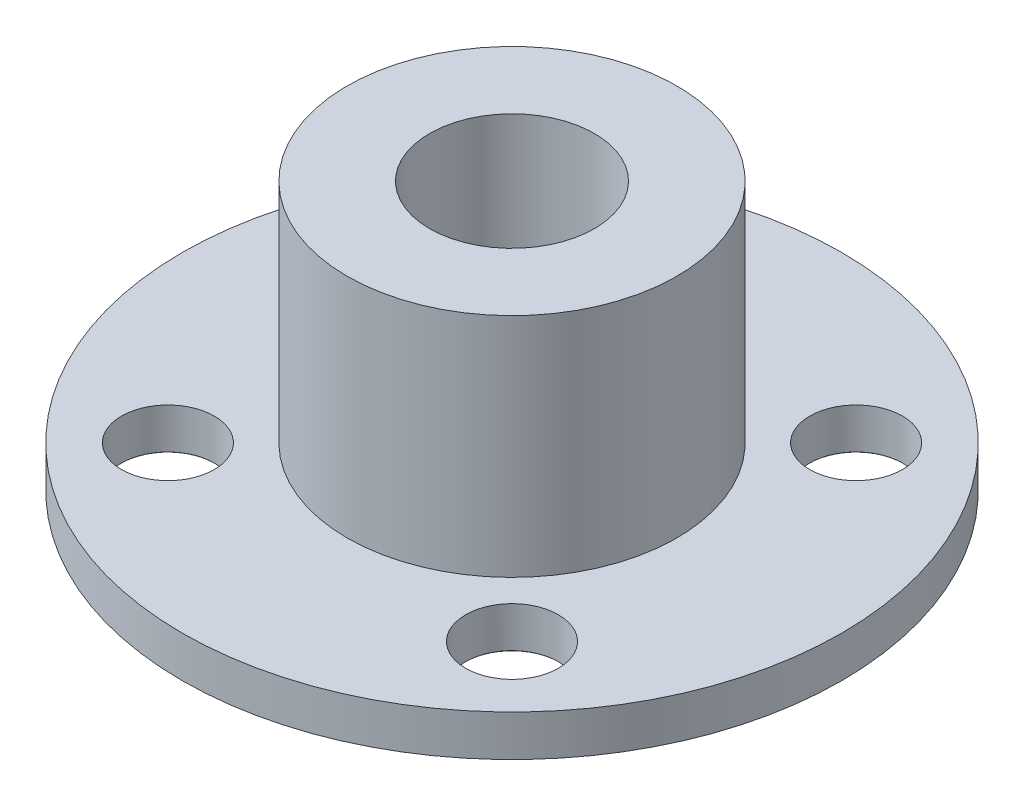
SolidWorks part; units mm, degrees
ref_plane "Front Plane" through (0, 0, 0) normal (0, 0, 1) x (1, 0, 0)
ref_plane "Top Plane" through (0, 0, 0) normal (0, 1, 0) x (1, 0, 0)
ref_plane "Right Plane" through (0, 0, 0) normal (1, 0, 0) x (0, 0, -1)
sketch "Sketch1" plane through (0, 0, 0) normal (0, 1, 0) x (1, 0, 0)
  circle A0 centre (0, 0) radius 16
  circle A1 centre (0, 0) radius 4
  dimension "D1" = 32
  dimension "D2" = 8
extrude "Boss-Extrude1" add sketch "Sketch1" along normal blind 2
sketch "Sketch2" plane through (0, 2, 0) normal (0, 1, 0) x (1, 0, 0)
  circle A0 centre (0, 0) radius 4
  circle A1 centre (0, 0) radius 8
  dimension "D1" = 8
  dimension "D2" = 16
extrude "Boss-Extrude2" add sketch "Sketch2" along normal blind 11 contours A1 | A0
hole_wizard "M4 Clearance Hole1" positions "Sketch5" profile "Sketch4" hole size "M4" standard "ANSI Metric"
sketch "Sketch5" plane through (0, 0, 0) normal (0, -1, 0) x (-1, 0, 0)
  point P0 (-8.35, 8.35)
  point P2 (8.35, 8.35)
  point P4 (8.35, -8.35)
  point P6 (-8.35, -8.35)
  dimension "D1" = 8.35
  dimension "D2" = 8.35
  dimension "D3" = 8.35
  dimension "D4" = 8.35
sketch "Sketch4" plane through (8.35, 0, -8.35) normal (1, 0, 0) x (0, 0, -1)
  line L0 (0, 0) -> (0, 14.3519)
  line L1 (0, 14.3519) -> (2.25, 13)
  line L2 (2.25, 13) -> (2.25, 0.025)
  line L3 (2.25, 0.025) -> (2.275, 0)
  line L5 (2.275, 0) -> (0, 0)
  line L6 (-2.25, 0.025) -> (-2.275, 0) construction
  line L10 (0, 14.3519) -> (-2.25, 13) construction
  line L11 (0, -6.35) -> (0, 107.95) construction
  dimension "Hole Dia." = 4.5
  dimension "Hole Depth" = 13
  dimension "Near C'Sink Dia." = 4.55
  dimension "Near C'Sink Angle" = 90
  dimension "Drill Angle" = 118
